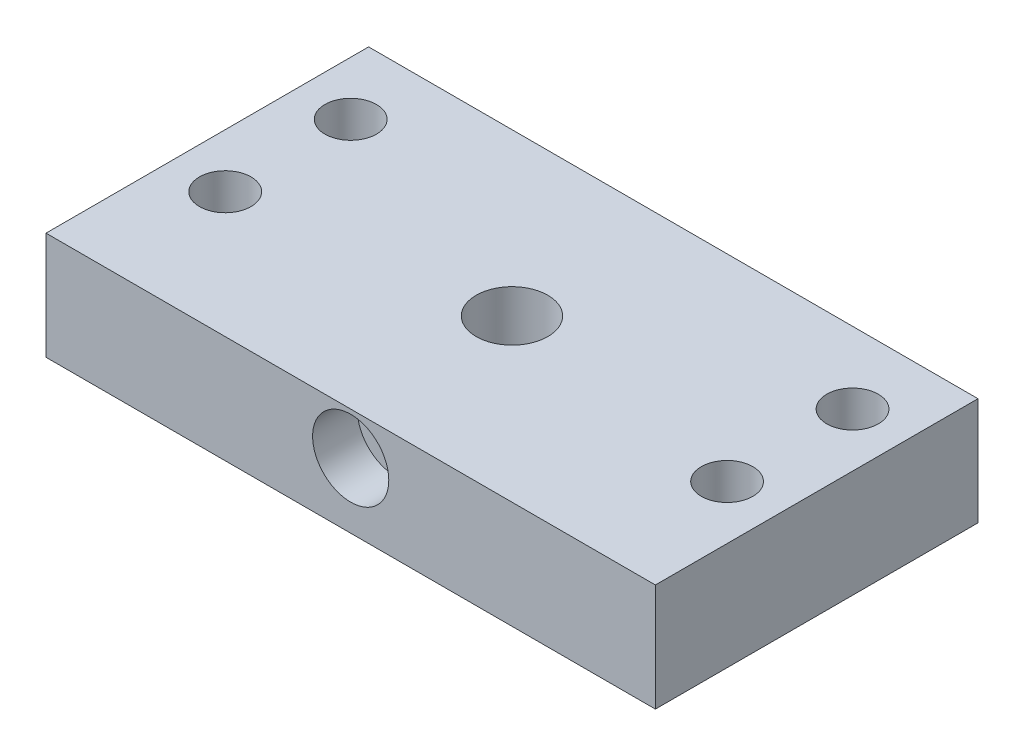
SolidWorks part; units mm, degrees
ref_plane "Front Plane" through (0, 0, 0) normal (0, 0, 1) x (1, 0, 0)
ref_plane "Top Plane" through (0, 0, 0) normal (0, 1, 0) x (1, 0, 0)
ref_plane "Right Plane" through (0, 0, 0) normal (1, 0, 0) x (0, 0, -1)
sketch "Sketch1" plane through (0, 0, 0) normal (0, 1, 0) x (1, 0, 0)
  line L1 (-34, -18) -> (34, -18)
  line L2 (-34, -18) -> (-34, 18)
  line L3 (-34, 18) -> (34, 18)
  line L4 (34, -18) -> (34, 18)
  line L5 (-34, -18) -> (34, 18) construction
  line L6 (-34, 18) -> (34, -18) construction
  point P0 (0, 0)
  dimension "D1" = 36
  dimension "D2" = 68
extrude "Boss-Extrude1" add sketch "Sketch1" along normal blind 12
sketch "Sketch2" plane through (0, 0, 0) normal (0, -1, 0) x (1, 0, 0)
  circle A0 centre (0, 0) radius 11
  dimension "D1" = 22
extrude "Cut-Extrude1" cut sketch "Sketch2" against normal blind 4
sketch "Sketch3" plane through (0, 4, 0) normal (0, -1, 0) x (1, 0, 0)
  circle A0 centre (0, 0) radius 4
  dimension "D1" = 8
extrude "Cut-Extrude2" cut sketch "Sketch3" against normal through all
sketch "Sketch4" plane through (0, 0, 18) normal (0, 0, 1) x (1, 0, 0)
  line L0 (-34, 12) -> (34, 12) construction
  circle A0 centre (0, 7.25) radius 2.375
  dimension "D1" = 4.75
  dimension "D2" = 4.75
extrude "Cut-Extrude3" cut sketch "Sketch4" against normal up to next
sketch "Sketch5" plane through (0, 0, 0) normal (0, -1, 0) x (1, 0, 0)
  line L1 (34, -18) -> (-34, -18) construction
  line L2 (34, 18) -> (34, -18) construction
  line L3 (-34, -18) -> (-34, 18) construction
  circle A0 centre (28, 4) radius 2.875
  circle A1 centre (28, -10) radius 2.875
  circle A2 centre (-28, 4) radius 2.875
  circle A3 centre (-28, -10) radius 2.875
  point P2 (0, 0)
  point P3 (0, 0)
  dimension "D1" = 5.75
  dimension "D3" = 5.75
  dimension "D5" = 5.75
  dimension "D6" = 5.75
  dimension "D2" = 14
  dimension "D4" = 8
  dimension "D7" = 6
  dimension "D8" = 6
  dimension "D9" = 6
  dimension "D10" = 6
  dimension "D11" = 8
  dimension "D12" = 14
extrude "Cut-Extrude4" cut sketch "Sketch5" against normal up to next
sketch "Sketch6" plane through (0, 0, 0) normal (0, -1, 0) x (1, 0, 0)
  circle A0 centre (-28, 4) radius 5
  circle A1 centre (28, 4) radius 5
  circle A2 centre (28, -10) radius 5
  circle A3 centre (-28, -10) radius 5
  dimension "D1" = 10
  dimension "D2" = 10
  dimension "D3" = 10
  dimension "D4" = 10
extrude "Cut-Extrude5" cut sketch "Sketch6" against normal blind 6
sketch "Sketch7" plane through (0, 0, 18) normal (0, 0, 1) x (1, 0, 0)
  circle A0 centre (0, 7.25) radius 4.25
  dimension "D1" = 8.5
extrude "Cut-Extrude6" cut sketch "Sketch7" against normal blind 5
